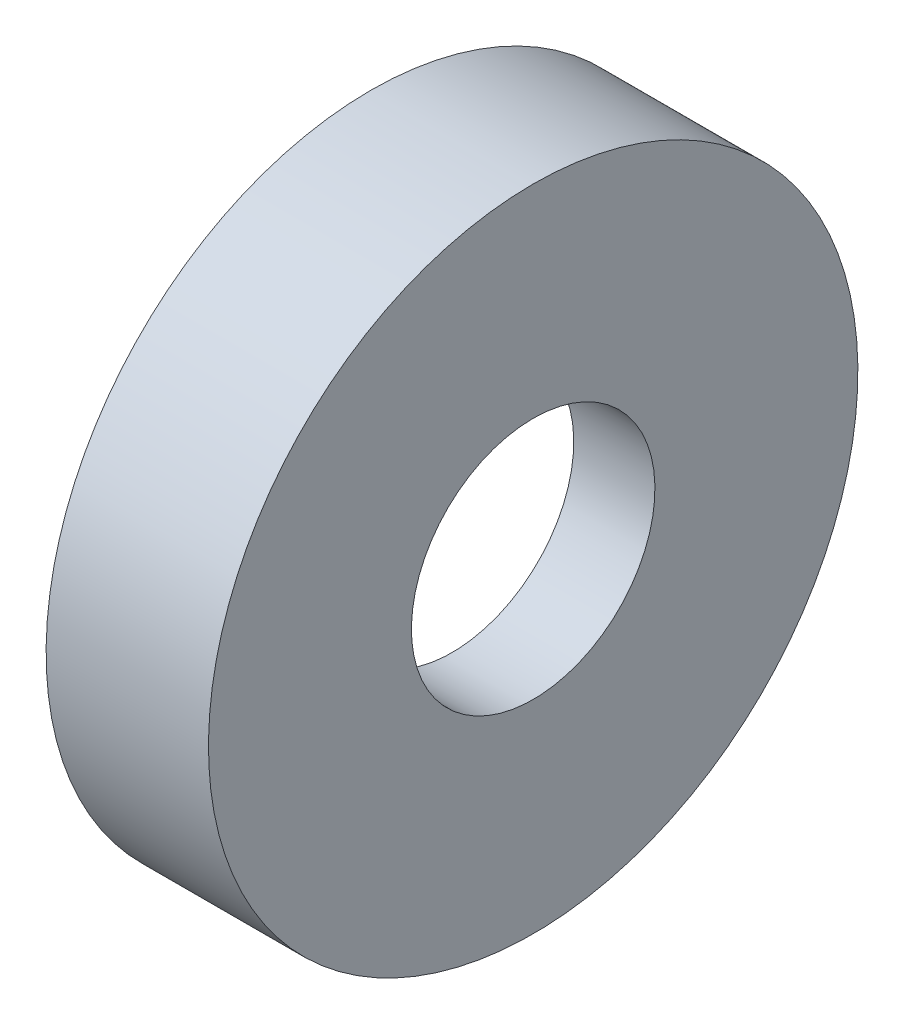
SolidWorks part; units mm, degrees
material "Nylon 101"
ref_plane "Front Plane" through (0, 0, 0) normal (0, 0, 1) x (1, 0, 0)
ref_plane "Top Plane" through (0, 0, 0) normal (0, 1, 0) x (1, 0, 0)
ref_plane "Right Plane" through (0, 0, 0) normal (1, 0, 0) x (0, 0, -1)
sketch "Sketch1" plane through (0, 0, 0) normal (0, 0, 1) x (1, 0, 0)
  line L0 (3.175, 0) -> (-3.175, 0) construction
  line L1 (-3.175, 0) -> (-3.175, 12.7) construction
  line L2 (-3.175, 12.7) -> (3.175, 12.7)
  line L3 (3.175, 12.7) -> (3.175, 0) construction
  line L4 (-3.175, 12.7) -> (-3.175, 11.1125)
  line L5 (-3.175, 11.1125) -> (0, 11.1125)
  line L6 (0, 11.1125) -> (0, 4.7625)
  line L7 (0, 4.7625) -> (3.175, 4.7625)
  line L8 (3.175, 12.7) -> (3.175, 4.7625)
  point P4 (0, 0)
  dimension "D1" = 25.4
  dimension "D2" = 22.225
  dimension "D3" = 9.525
  dimension "D4" = 6.35
  dimension "D5" = 3.175
revolve "Revolve1" add sketch "Sketch1" angle 360 about L0
